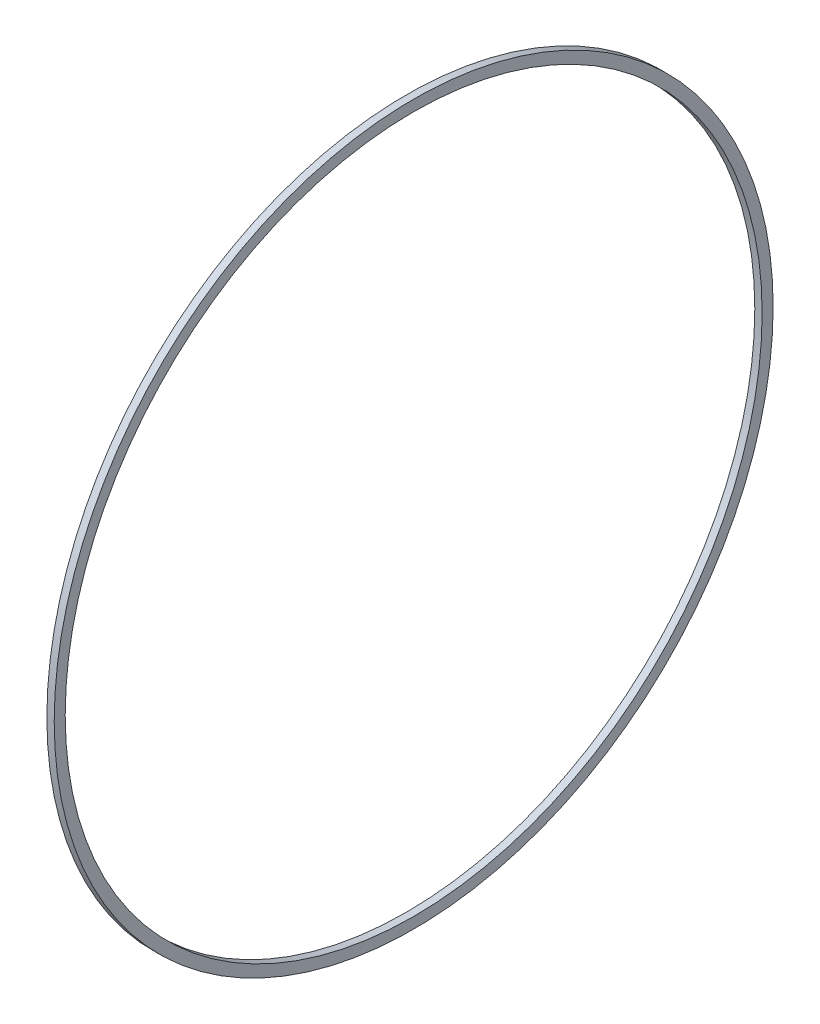
SolidWorks part; units mm, degrees
material "1060-O (SS)"
ref_plane "Ebene vorne" through (0, 0, 0) normal (0, 0, 1) x (1, 0, 0)
ref_plane "Ebene oben" through (0, 0, 0) normal (0, 1, 0) x (1, 0, 0)
ref_plane "Ebene rechts" through (0, 0, 0) normal (1, 0, 0) x (0, 0, -1)
sketch "Sketch1" plane through (0, 0, 0) normal (1, 0, 0) x (0, 0, -1)
  circle A0 centre (0, 0) radius 47.5
  circle A1 centre (0, 0) radius 49
  dimension "D1" = 98
  dimension "D2" = 1.5
extrude "Boss-Extrude1" add sketch "Sketch1" along normal blind 1
